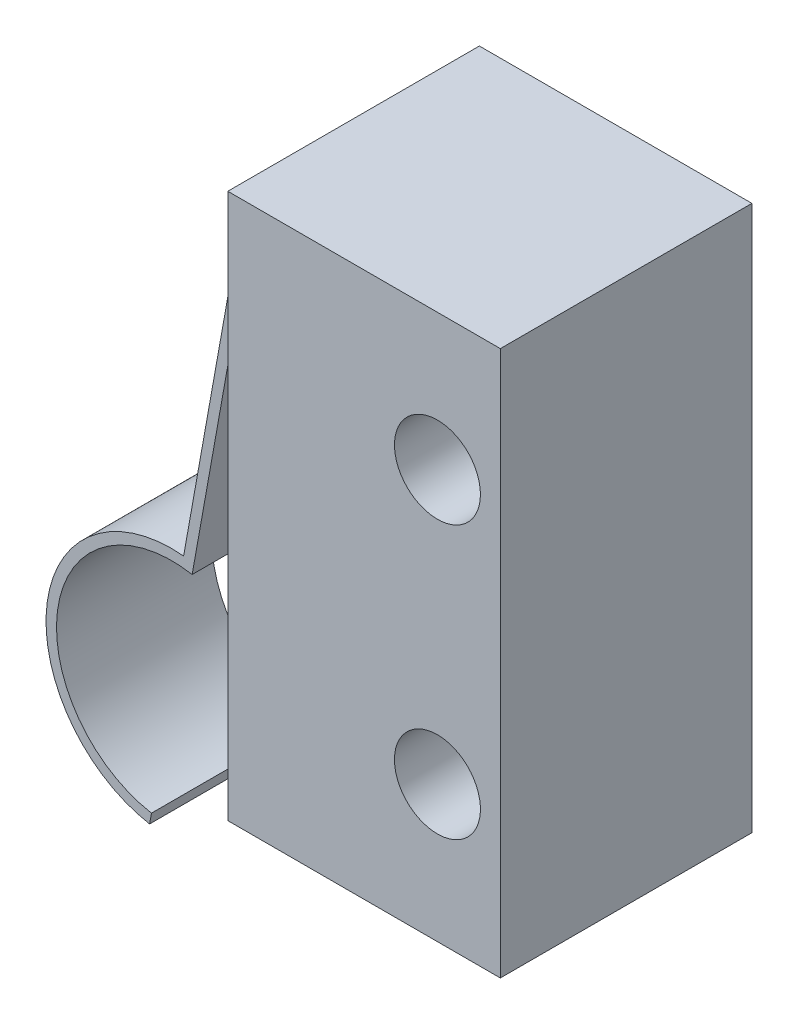
SolidWorks part; units mm, degrees
ref_plane "Front Plane" through (0, 0, 0) normal (0, 0, 1) x (1, 0, 0)
ref_plane "Top Plane" through (0, 0, 0) normal (0, 1, 0) x (1, 0, 0)
ref_plane "Right Plane" through (0, 0, 0) normal (1, 0, 0) x (0, 0, -1)
sketch "Sketch1" plane through (0, 0, 0) normal (0, 0, 1) x (1, 0, 0)
  line L1 (-3.25, 6.5) -> (3.25, 6.5)
  line L2 (-3.25, 6.5) -> (-3.25, -6.5)
  line L3 (-3.25, -6.5) -> (3.25, -6.5)
  line L4 (3.25, 6.5) -> (3.25, -6.5)
  line L5 (-3.25, 6.5) -> (3.25, -6.5) construction
  line L6 (-3.25, -6.5) -> (3.25, 6.5) construction
  point P0 (0, 0)
  dimension "D1" = 13
  dimension "D2" = 6.5
extrude "Boss-Extrude1" add sketch "Sketch1" along normal mid plane 6
sketch "Sketch4" plane through (0, 0, 3) normal (0, 0, 1) x (1, 0, 0)
  line L0 (-3.25, 0) -> (3.25, 0) construction
  line L1 (-3.25, 6.5) -> (-3.25, -6.5) construction
  line L2 (3.25, -6.5) -> (3.25, 6.5) construction
  circle A0 centre (1.75, 3.25) radius 1.025
  circle A1 centre (1.75, -3.25) radius 1.025
  dimension "D2" = 2.05
  dimension "D1" = 5
  dimension "D3" = 6.5
extrude "Cut-Extrude1" cut sketch "Sketch4" against normal through all
sketch "Sketch8" plane through (-3.25, 0, 0) normal (-1, 0, 0) x (0, 0, 1)
  line L0 (3, 6.5) -> (-3, 6.5) construction
  line L1 (-1.85, 5.5) -> (1.85, 5.5)
  line L2 (-1.85, 5.5) -> (-1.85, 5.25)
  line L3 (-1.85, 5.25) -> (1.85, 5.25)
  line L4 (1.85, 5.5) -> (1.85, 5.25)
  line L5 (-1.85, 5.5) -> (1.85, 5.25) construction
  line L6 (-1.85, 5.25) -> (1.85, 5.5) construction
  point P0 (0, 5.375)
  dimension "D1" = 1
  dimension "D2" = 0.25
  dimension "D3" = 3.7
sketch "Sketch9" plane through (0, 0, 0) normal (0, 0, 1) x (1, 0, 0)
  line L0 (-3.25, 5.375) -> (-3.75, 5.375)
  line L1 (-3.75, 5.375) -> (-5.25, -2.9916)
  line L2 (-3.25, 6.5) -> (-3.25, -6.5) construction
  arc A0 (-5.25, -2.9916) -> (-6.2206, -8.4053) centre (-5.7353, -5.6984) ccw
  dimension "D1" = 0.5
  dimension "D2" = 8.5
  dimension "D3" = 5.5
  dimension "D4" = 2
extrude "Extrude-Thin1" add sketch "Sketch9" along normal mid plane 3.7 thin
